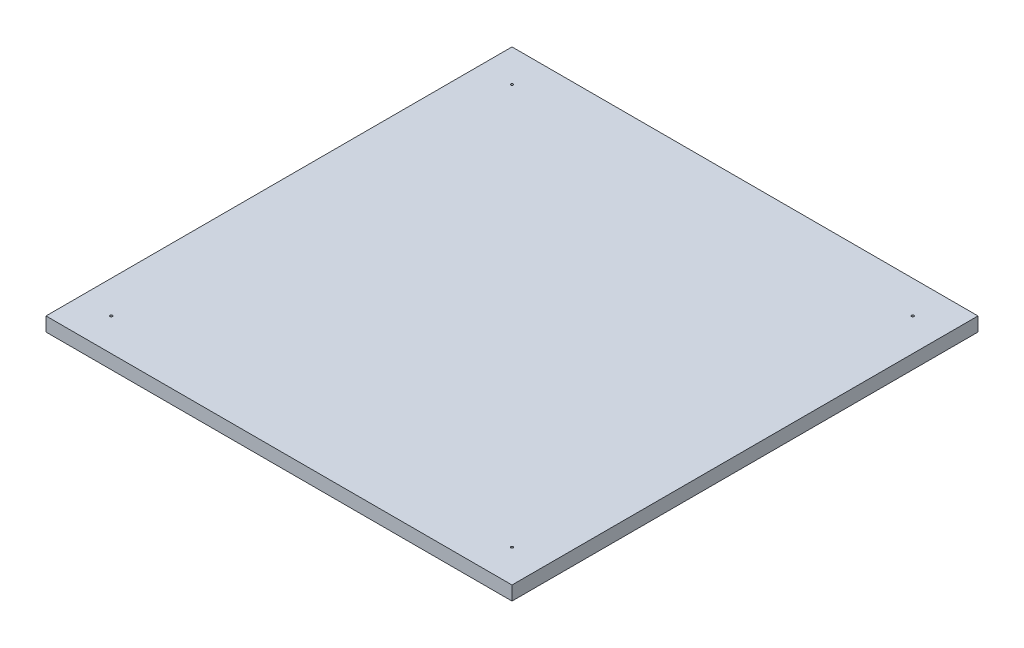
SolidWorks part; units mm, degrees
ref_plane "Front Plane" through (0, 0, 0) normal (0, 0, 1) x (1, 0, 0)
ref_plane "Top Plane" through (0, 0, 0) normal (0, 1, 0) x (1, 0, 0)
ref_plane "Right Plane" through (0, 0, 0) normal (1, 0, 0) x (0, 0, -1)
sketch "Sketch1" plane through (0, 0, 0) normal (1, 0, 0) x (0, 0, -1)
  line L0 (0, 0) -> (1000, 0)
  line L1 (1000, 30) -> (0, 30)
  line L2 (0, 30) -> (0, 0)
  line L3 (1000, 30) -> (1000, 0)
  dimension "D1" = 30
  dimension "D2" = 1000
extrude "Boss-Extrude1" add sketch "Sketch1" along normal mid plane 1000
sketch "Sketch2" plane through (0, 30, 0) normal (0, 1, 0) x (1, 0, 0)
  line L0 (500, 0) -> (-500, 0) construction
  line L1 (500, 1000) -> (-500, 1000) construction
  line L2 (-500, 1000) -> (-500, 0) construction
  line L3 (500, 1000) -> (500, 0) construction
  circle A0 centre (-430, 70) radius 2.5
  circle A1 centre (-430, 930) radius 2.5
  circle A2 centre (430, 930) radius 2.5
  circle A3 centre (430, 70) radius 2.5
  dimension "D1" = 5
  dimension "D2" = 5
  dimension "D3" = 5
  dimension "D4" = 5
  dimension "D5" = 70
  dimension "D6" = 70
  dimension "D7" = 70
  dimension "D8" = 70
  dimension "D9" = 70
  dimension "D10" = 70
  dimension "D11" = 70
  dimension "D12" = 70
  dimension "D13" = 70
extrude "Cut-Extrude2" cut sketch "Sketch2" against normal blind 5
